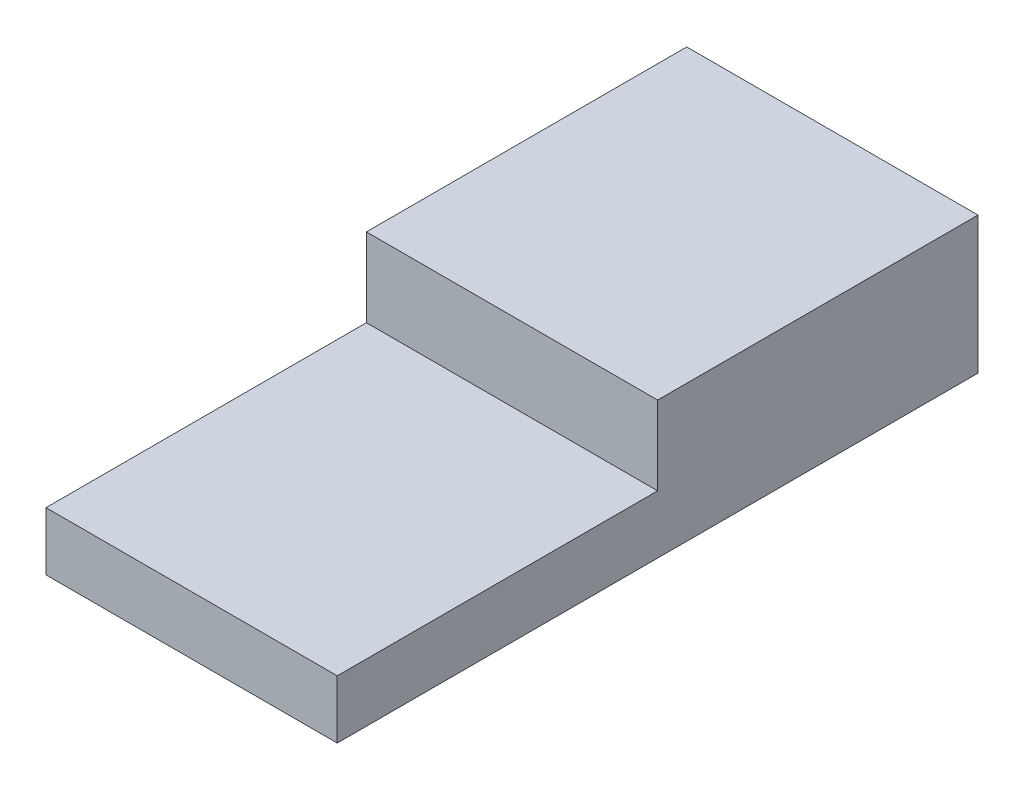
SolidWorks part; units mm, degrees
ref_plane "Front Plane" through (0, 0, 0) normal (0, 0, 1) x (1, 0, 0)
ref_plane "Top Plane" through (0, 0, 0) normal (0, 1, 0) x (1, 0, 0)
ref_plane "Right Plane" through (0, 0, 0) normal (1, 0, 0) x (0, 0, -1)
sketch "Sketch3" plane through (0, 0, 0) normal (0, 1, 0) x (1, 0, 0)
  line L1 (-17.8498, 2.5305) -> (-7.8498, 2.5305)
  line L2 (-17.8498, 2.5305) -> (-17.8498, -19.4695)
  line L3 (-17.8498, -19.4695) -> (-7.8498, -19.4695)
  line L4 (-7.8498, 2.5305) -> (-7.8498, -19.4695)
  dimension "D1" = 22
  dimension "D2" = 10
extrude "Boss-Extrude1" add sketch "Sketch3" along normal blind 2
sketch "Sketch4" plane through (0, 2, 0) normal (0, 1, 0) x (1, 0, 0)
  line L0 (-7.8498, -19.4695) -> (-7.8498, 2.5305) construction
  line L1 (-17.8498, 2.5305) -> (-7.8498, 2.5305)
  line L2 (-17.8498, 2.5305) -> (-17.8498, -8.4695)
  line L3 (-17.8498, -8.4695) -> (-7.8498, -8.4695)
  line L4 (-7.8498, 2.5305) -> (-7.8498, -8.4695)
  dimension "11" = 11
extrude "Boss-Extrude2" add sketch "Sketch4" along normal blind 2.7
sketch "Sketch5" plane through (-17.8498, 0, 0) normal (-1, 0, 0) x (0, 0, 1)
  line L0 (-2.5305, 4.7) -> (-2.5305, 0) construction
  line L1 (-2.5305, 0) -> (19.4695, 0) construction
  circle A0 centre (3.3695, 2.3) radius 1
  point P4 (0, 0)
  dimension "D2" = 2
  dimension "D1" = 5.9
  dimension "D3" = 2.3
extrude "Cut-Extrude1" cut sketch "Sketch5" against normal blind 2
